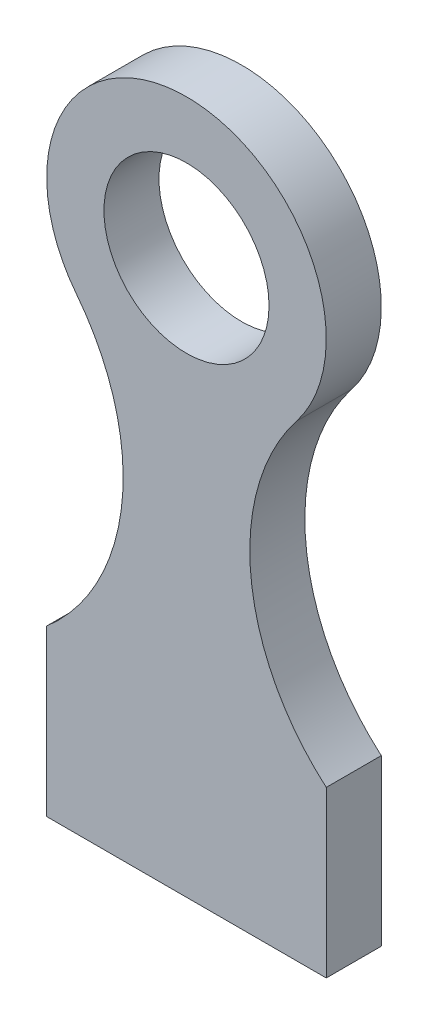
SolidWorks part; units mm, degrees
ref_plane "Front Plane" through (0, 0, 0) normal (0, 0, 1) x (1, 0, 0)
ref_plane "Top Plane" through (0, 0, 0) normal (0, 1, 0) x (1, 0, 0)
ref_plane "Right Plane" through (0, 0, 0) normal (1, 0, 0) x (0, 0, -1)
sketch "Sketch1" plane through (0, 0, 0) normal (0, 0, 1) x (1, 0, 0)
  line L0 (0.8767, 3.2822) -> (0.8767, -3.0178) construction
  line L1 (-0.3933, -1.5178) -> (2.1467, -1.5178) construction
  line L3 (-0.3933, -3.0178) -> (2.1467, -3.0178)
  line L4 (2.1467, -1.5178) -> (2.1467, -3.0178)
  line L5 (-0.3933, -1.5178) -> (-0.3933, -3.0178)
  arc A0 (1.8769, 1.2297) -> (-0.1236, 1.2297) centre (0.8767, 2.0122) ccw
  circle A1 centre (0.8767, 2.0122) radius 0.75
  arc A2 (-0.3933, -1.5178) -> (-0.1236, 1.2297) centre (-1.6988, -0.0026) ccw
  arc A3 (2.1467, -1.5178) -> (1.8769, 1.2297) centre (3.4522, -0.0026) cw
  dimension "D3" = 1.5
  dimension "D2" = 4
  dimension "D5" = 2.54
  dimension "D6" = 6.3
  dimension "D1" = 1.5
  dimension "D4" = 5.03
extrude "Boss-Extrude1" add sketch "Sketch1" along normal blind 0.5
